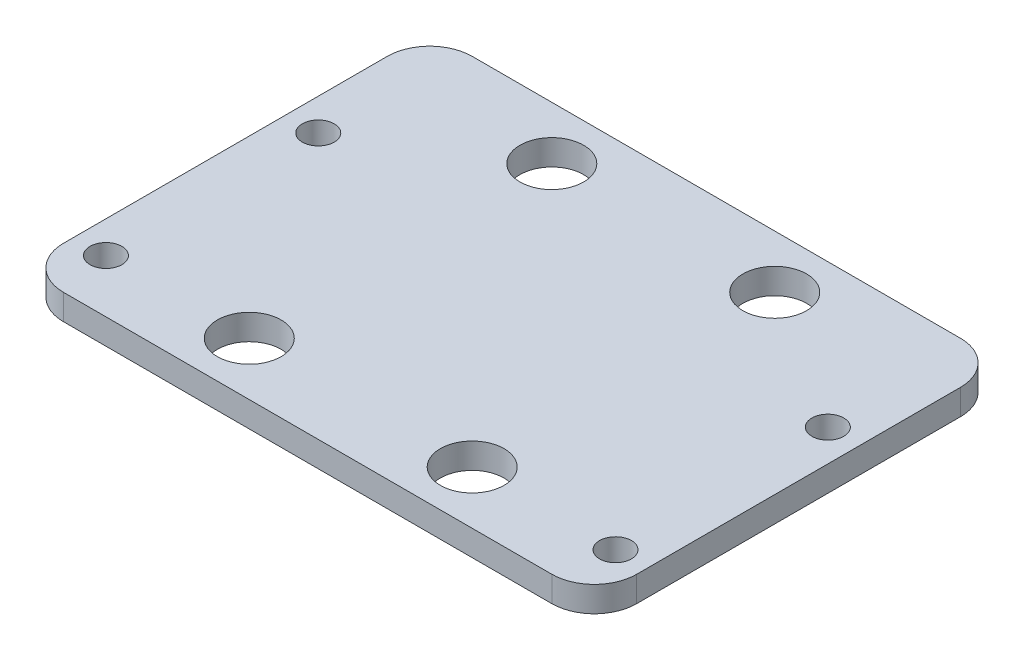
SolidWorks part; units mm, degrees
ref_plane "前基準面" through (0, 0, 0) normal (0, 0, 1) x (1, 0, 0)
ref_plane "上基準面" through (0, 0, 0) normal (0, 1, 0) x (1, 0, 0)
ref_plane "右基準面" through (0, 0, 0) normal (1, 0, 0) x (0, 0, -1)
sketch "草圖1" plane through (0, 0, 0) normal (0, 1, 0) x (1, 0, 0)
  line L0 (0, -9.5833) -> (0, 9.5833) construction
  line L1 (-40.4352, 0) -> (40.4352, 0) construction
  line L3 (-27, 33.5) -> (27, 33.5)
  line L4 (-27, 33.5) -> (-27, -5)
  line L5 (-27, -5) -> (27, -5)
  line L6 (27, 33.5) -> (27, -5)
  line L7 (0, -5) -> (0, 33.5) construction
  line L8 (-27, 14.25) -> (27, 14.25) construction
  circle A0 centre (-24, 0) radius 1.5
  circle A1 centre (24, 0) radius 1.5
  circle A2 centre (-10.5, 28.5) radius 3
  circle A3 centre (10.5, 28.5) radius 3
  circle A4 centre (-10.5, 0) radius 3
  circle A5 centre (10.5, 0) radius 3
  circle A6 centre (24, 20) radius 1.5
  circle A7 centre (-24, 20) radius 1.5
  point P4 (0, 0)
  point P10 (0, 14.25)
  point P12 (0, 0)
  point P22 (19.1445, 22.6229)
  point P27 (10.5, 0)
  dimension "D1" = 3
  dimension "D3" = 6
  dimension "D2" = 48
  dimension "D4" = 21
  dimension "D5" = 28.5
  dimension "D6" = 5
  dimension "D7" = 3
  dimension "D9" = 20
  dimension "D8" = 2
extrude "填料-伸長1" add sketch "草圖1" along normal blind 2.4
fillet "圓角1" radius 4 4 edges at (27, 1.2, -33.5) (-27, 1.2, -33.5) (-27, 1.2, 5) (27, 1.2, 5)
